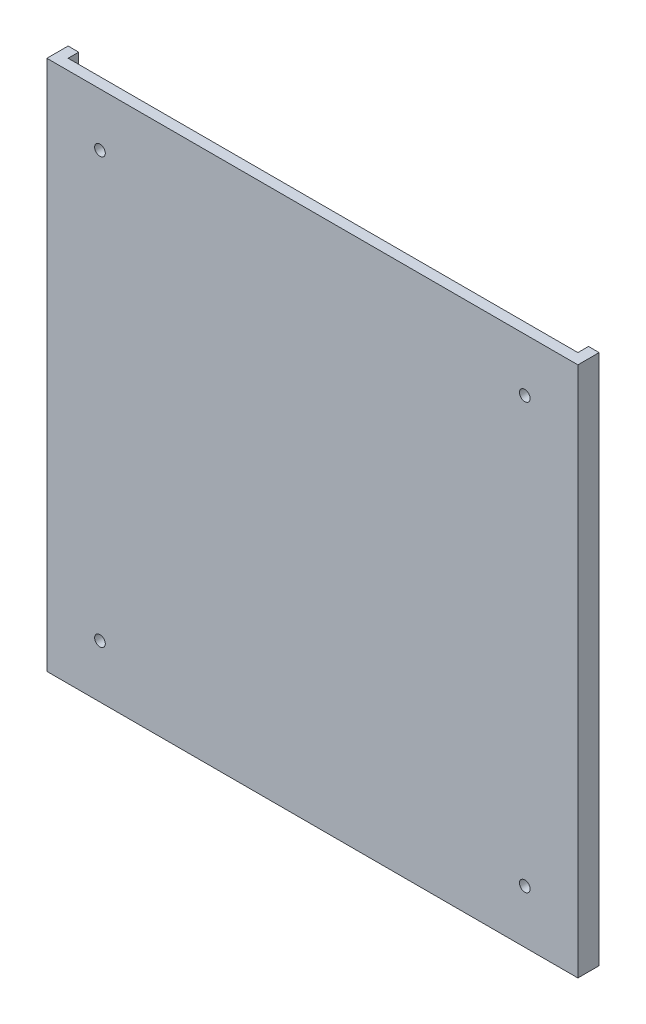
SolidWorks part; units mm, degrees
ref_plane "Front Plane" through (0, 0, 0) normal (0, 0, 1) x (1, 0, 0)
ref_plane "Top Plane" through (0, 0, 0) normal (0, 1, 0) x (1, 0, 0)
ref_plane "Right Plane" through (0, 0, 0) normal (1, 0, 0) x (0, 0, -1)
sketch "Sketch1" plane through (0, 0, 0) normal (0, 0, 1) x (1, 0, 0)
  line L1 (-250, -250) -> (250, -250)
  line L2 (-250, -250) -> (-250, 250)
  line L3 (-250, 250) -> (250, 250)
  line L4 (250, -250) -> (250, 250)
  line L5 (-250, -250) -> (250, 250) construction
  line L6 (-250, 250) -> (250, -250) construction
  point P0 (0, 0)
  dimension "D1" = 500
  dimension "D2" = 500
extrude "Boss-Extrude1" add sketch "Sketch1" along normal blind 20
sketch "Sketch2" plane through (0, 250, 0) normal (0, 1, 0) x (1, 0, 0)
  line L0 (250, 0) -> (-250, 0) construction
  line L1 (-240, 0) -> (240, 0)
  line L2 (-240, 0) -> (-240, -10)
  line L3 (-240, -10) -> (240, -10)
  line L4 (240, 0) -> (240, -10)
  line L5 (-250, -20) -> (-250, 0) construction
  line L6 (250, -20) -> (-250, -20) construction
  line L7 (250, -20) -> (250, 0) construction
  dimension "D1" = 10
  dimension "D2" = 10
  dimension "D3" = 10
extrude "Cut-Extrude1" cut sketch "Sketch2" against normal blind 500
sketch "Sketch3" plane through (0, 0, 20) normal (0, 0, 1) x (1, 0, 0)
  line L0 (250, -250) -> (250, 250) construction
  line L1 (-250, 250) -> (-250, -250) construction
  line L2 (-250, -250) -> (250, -250) construction
  line L3 (250, 250) -> (-250, 250) construction
  circle A0 centre (-200, 200) radius 5
  circle A1 centre (200, 200) radius 5
  circle A2 centre (-200, -200) radius 5
  circle A3 centre (200, -200) radius 5
  dimension "D1" = 10
  dimension "D2" = 50
  dimension "D3" = 50
  dimension "D4" = 50
  dimension "D5" = 50
extrude "Cut-Extrude2" cut sketch "Sketch3" against normal blind 10
